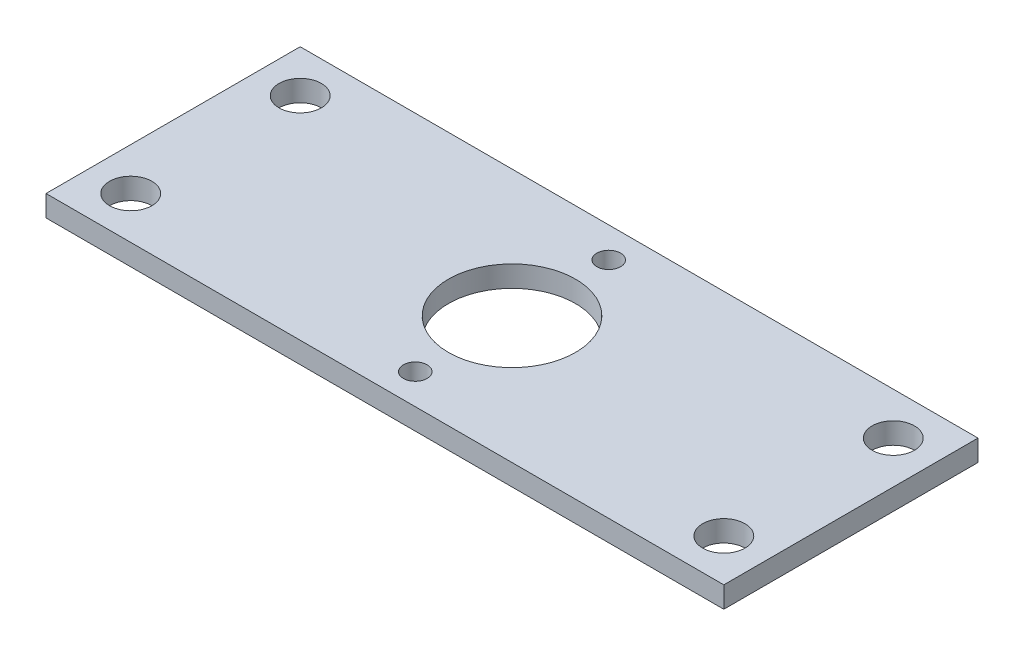
SolidWorks part; units mm, degrees
material "6061-T6 (SS)"
ref_plane "Front Plane" through (0, 0, 0) normal (0, 0, 1) x (1, 0, 0)
ref_plane "Top Plane" through (0, 0, 0) normal (0, 1, 0) x (1, 0, 0)
ref_plane "Right Plane" through (0, 0, 0) normal (1, 0, 0) x (0, 0, -1)
sketch "Sketch1" plane through (0, 0, 0) normal (0, 1, 0) x (1, 0, 0)
  line L1 (-12.7, 19.05) -> (12.7, 19.05)
  line L2 (-12.7, 19.05) -> (-12.7, -19.05)
  line L3 (-12.7, -19.05) -> (12.7, -19.05)
  line L4 (12.7, 19.05) -> (12.7, -19.05)
  line L5 (-12.7, 19.05) -> (12.7, -19.05) construction
  line L6 (-12.7, -19.05) -> (12.7, 19.05) construction
  point P0 (0, 0)
  dimension "D1" = 25.4
  dimension "D2" = 38.1
extrude "Boss-Extrude1" add sketch "Sketch1" along normal blind 3.175
sketch "Sketch2" plane through (0, 3.175, 0) normal (0, 1, 0) x (1, 0, 0)
  line L0 (-4.7625, -14.5) -> (4.7625, -14.5) construction
  line L1 (-4.7625, -12.722) -> (4.7625, -12.722) construction
  line L2 (-4.7625, -16.278) -> (4.7625, -16.278) construction
  line L3 (4.7625, 14.5) -> (-4.7625, 14.5) construction
  line L4 (4.7625, 12.722) -> (-4.7625, 12.722) construction
  line L5 (4.7625, 16.278) -> (-4.7625, 16.278) construction
  line L6 (-4.7625, 0) -> (-12.7, 0) construction
  line L7 (-12.7, 19.05) -> (-4.7625, 14.5) construction
  line L8 (-4.7625, -14.5) -> (-12.7, -19.05) construction
  line L9 (4.7625, 0) -> (-4.7625, 0) construction
  line L10 (4.7625, -9.525) -> (-4.7625, -9.525) construction
  line L11 (4.7625, 9.525) -> (-4.7625, 9.525) construction
  line L12 (4.7625, 0) -> (12.7, 0) construction
  line L14 (-12.7, 19.05) -> (-12.7, -19.05) construction
  line L15 (12.7, -19.05) -> (12.7, 19.05) construction
  arc A0 (-4.7625, -12.722) -> (-4.7625, -16.278) centre (-4.7625, -14.5) ccw construction
  arc A1 (4.7625, -16.278) -> (4.7625, -12.722) centre (4.7625, -14.5) ccw construction
  arc A2 (4.7625, 12.722) -> (4.7625, 16.278) centre (4.7625, 14.5) ccw construction
  arc A3 (-4.7625, 16.278) -> (-4.7625, 12.722) centre (-4.7625, 14.5) ccw construction
  circle A4 centre (-44.45, 14.5) radius 1.65 construction
  arc A5 (4.7625, -9.525) -> (4.7625, 9.525) centre (4.7625, 0) ccw construction
  arc A6 (-4.7625, 9.525) -> (-4.7625, -9.525) centre (-4.7625, 0) ccw construction
  circle A7 centre (0, 0) radius 9.525
  circle A8 centre (0, -14.5) radius 1.778
  circle A9 centre (0, 14.5) radius 1.778
  point P2 (0, -14.5)
  point P7 (0, 14.5)
  point P16 (-44.45, 14.5)
  point P22 (0, 0)
  point P46 (-13.335, 0)
  point P47 (4.7625, 0)
  dimension "D2" = 9.525
  dimension "D1" = 3.556
  dimension "D4" = 19.05
extrude "Cut-Extrude1" cut sketch "Sketch2" against normal blind 3.175
sketch "Sketch3" plane through (-12.7, 0, 0) normal (-1, 0, 0) x (0, 0, 1)
  line L1 (-19.05, 0) -> (19.05, 0)
  line L2 (-19.05, 0) -> (-19.05, 3.175)
  line L3 (-19.05, 3.175) -> (19.05, 3.175)
  line L4 (19.05, 0) -> (19.05, 3.175)
extrude "Boss-Extrude2" add sketch "Sketch3" along normal blind 38.1
sketch "Sketch6" plane through (12.7, 0, 0) normal (1, 0, 0) x (0, 0, -1)
  line L1 (-19.05, 0) -> (19.05, 0)
  line L2 (-19.05, 0) -> (-19.05, 3.175)
  line L3 (-19.05, 3.175) -> (19.05, 3.175)
  line L4 (19.05, 0) -> (19.05, 3.175)
extrude "Boss-Extrude4" add sketch "Sketch6" along normal blind 38.1
sketch "Sketch4" plane through (0, 3.175, 0) normal (0, 1, 0) x (1, 0, 0)
  line L0 (-44.45, -12.7) -> (-50.8, -19.05) construction
  line L1 (-50.8, 19.05) -> (-44.45, 12.7) construction
  line L2 (44.45, -12.7) -> (44.45, -19.05) construction
  line L4 (-50.8, -19.05) -> (50.8, -19.05) construction
  line L5 (-50.8, -19.05) -> (-50.8, 19.05) construction
  line L6 (-50.8, -12.7) -> (-44.45, -12.7) construction
  line L7 (-44.45, -12.7) -> (-44.45, -19.05) construction
  line L8 (-50.8, -19.05) -> (50.8, -19.05) construction
  line L9 (44.45, -12.7) -> (50.8, -12.7) construction
  line L10 (50.8, 19.05) -> (50.8, -19.05) construction
  circle A0 centre (-44.45, 12.7) radius 3.175
  circle A1 centre (-44.45, -12.7) radius 3.175
  circle A2 centre (44.45, -12.7) radius 3.175
  circle A3 centre (44.45, 12.7) radius 3.175
  dimension "D1" = 25.4
  dimension "D2" = 6.35
extrude "Cut-Extrude2" cut sketch "Sketch4" against normal through all
